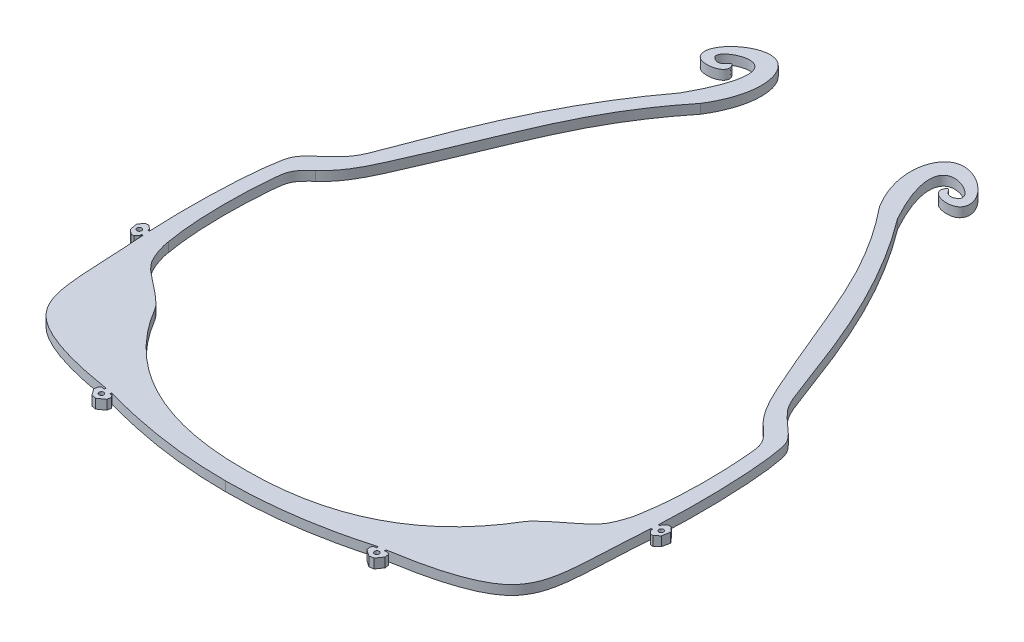
SolidWorks part; units mm, degrees
ref_plane "Front Plane" through (0, 0, 0) normal (0, 0, 1) x (1, 0, 0)
ref_plane "Top Plane" through (0, 0, 0) normal (0, 1, 0) x (1, 0, 0)
ref_plane "Right Plane" through (0, 0, 0) normal (1, 0, 0) x (0, 0, -1)
sketch "Sketch1" plane through (0, 0, 0) normal (0, 1, 0) x (1, 0, 0)
  line L0 (-56.7342, 4649.685) -> (-54.3432, 4649.8666)
  line L1 (-54.3432, 4649.8666) -> (-51.9673, 4650.1279)
  line L2 (-51.9673, 4650.1279) -> (-49.6128, 4650.4904)
  line L3 (-49.6128, 4650.4904) -> (-47.2873, 4650.9763)
  line L4 (-47.2873, 4650.9763) -> (-45.0028, 4651.606)
  line L5 (-45.0028, 4651.606) -> (-42.7754, 4652.393)
  line L6 (-42.7754, 4652.393) -> (-40.6236, 4653.3398)
  line L7 (-40.6236, 4653.3398) -> (-38.5569, 4654.4471)
  line L8 (-38.5569, 4654.4471) -> (-36.5628, 4655.7048)
  line L9 (-36.5628, 4655.7048) -> (-34.628, 4657.0886)
  line L10 (-34.628, 4657.0886) -> (-32.7572, 4658.5809)
  line L11 (-32.7572, 4658.5809) -> (-31.8781, 4659.3559)
  line L12 (-31.8781, 4659.3559) -> (-31.0378, 4660.1663)
  line L13 (-31.0378, 4660.1663) -> (-30.2434, 4661.0133)
  line L14 (-30.2434, 4661.0133) -> (-29.4929, 4661.8977)
  line L15 (-29.4929, 4661.8977) -> (-28.0377, 4663.8002)
  line L16 (-28.0377, 4663.8002) -> (-26.6418, 4665.7643)
  line L17 (-26.6418, 4665.7643) -> (-25.2842, 4667.7433)
  line L18 (-25.2842, 4667.7433) -> (-24.5616, 4668.7671)
  line L19 (-24.5616, 4668.7671) -> (-24.1207, 4669.3049)
  line L20 (-24.1207, 4669.3049) -> (-23.6287, 4669.8041)
  line L21 (-23.6287, 4669.8041) -> (-22.6527, 4670.6453)
  line L22 (-22.6527, 4670.6453) -> (-21.6624, 4671.4168)
  line L23 (-21.6624, 4671.4168) -> (-19.7154, 4672.8766)
  line L24 (-19.7154, 4672.8766) -> (-18.7888, 4673.6051)
  line L25 (-18.7888, 4673.6051) -> (-17.9151, 4674.3646)
  line L26 (-17.9151, 4674.3646) -> (-17.0961, 4675.1711)
  line L27 (-17.0961, 4675.1711) -> (-16.3332, 4676.0235)
  line L28 (-16.3332, 4676.0235) -> (-14.888, 4677.8872)
  line L29 (-14.888, 4677.8872) -> (-14.2651, 4678.8282)
  line L30 (-14.2651, 4678.8282) -> (-13.7395, 4679.8092)
  line L31 (-13.7395, 4679.8092) -> (-13.3157, 4680.8364)
  line L32 (-13.3157, 4680.8364) -> (-12.9921, 4681.9053)
  line L33 (-12.9921, 4681.9053) -> (-12.765, 4683.0137)
  line L34 (-12.765, 4683.0137) -> (-12.6116, 4684.156)
  line L35 (-12.6116, 4684.156) -> (-12.4221, 4686.5439)
  line L36 (-12.4221, 4686.5439) -> (-12.3049, 4688.9547)
  line L37 (-12.3049, 4688.9547) -> (-12.23, 4691.3606)
  line L38 (-12.23, 4691.3606) -> (-12.2173, 4693.7469)
  line L39 (-12.2173, 4693.7469) -> (-12.2979, 4696.128)
  line L40 (-12.2979, 4696.128) -> (-12.4621, 4698.525)
  line L41 (-12.4621, 4698.525) -> (-12.9016, 4703.3562)
  line L42 (-12.9016, 4703.3562) -> (-13.1725, 4705.7323)
  line L43 (-13.1725, 4705.7323) -> (-13.359, 4706.8497)
  line L44 (-13.359, 4706.8497) -> (-13.6464, 4707.8976)
  line L45 (-13.6464, 4707.8976) -> (-13.8331, 4708.3435)
  line L46 (-13.8331, 4708.3435) -> (-14.0727, 4708.7863)
  line L47 (-14.0727, 4708.7863) -> (-14.3603, 4709.2104)
  line L48 (-14.3603, 4709.2104) -> (-14.6922, 4709.6118)
  line L49 (-14.6922, 4709.6118) -> (-15.5352, 4710.4427)
  line L50 (-15.5352, 4710.4427) -> (-16.4733, 4711.2489)
  line L51 (-16.4733, 4711.2489) -> (-18.3969, 4712.8768)
  line L52 (-18.3969, 4712.8768) -> (-19.3317, 4713.7593)
  line L53 (-19.3317, 4713.7593) -> (-19.7964, 4714.2738)
  line L54 (-19.7964, 4714.2738) -> (-20.226, 4714.8564)
  line L55 (-20.226, 4714.8564) -> (-20.8491, 4716.0227)
  line L56 (-20.8491, 4716.0227) -> (-21.3607, 4717.2182)
  line L57 (-21.3607, 4717.2182) -> (-22.2565, 4719.6128)
  line L58 (-22.2565, 4719.6128) -> (-23.9365, 4724.4003)
  line L59 (-23.9365, 4724.4003) -> (-24.8142, 4726.6925)
  line L60 (-24.8142, 4726.6925) -> (-25.7235, 4728.951)
  line L61 (-25.7235, 4728.951) -> (-29.4192, 4737.978)
  line L62 (-29.4192, 4737.978) -> (-31.3112, 4742.476)
  line L63 (-31.3112, 4742.476) -> (-32.3108, 4744.6883)
  line L64 (-32.3108, 4744.6883) -> (-33.3653, 4746.8748)
  line L65 (-33.3653, 4746.8748) -> (-34.484, 4749.0197)
  line L66 (-34.484, 4749.0197) -> (-35.6822, 4751.1089)
  line L67 (-35.6822, 4751.1089) -> (-36.9697, 4753.1376)
  line L68 (-36.9697, 4753.1376) -> (-38.335, 4755.1176)
  line L69 (-38.335, 4755.1176) -> (-39.7566, 4757.0561)
  line L70 (-39.7566, 4757.0561) -> (-41.2239, 4758.9538)
  line L71 (-41.2239, 4758.9538) -> (-44.2837, 4762.6862)
  line L72 (-44.2837, 4762.6862) -> (-45.0093, 4763.5782)
  line L73 (-45.7102, 4766.0333) -> (-45.6003, 4766.895)
  line L74 (-44.3387, 4767.2717) -> (-41.5099, 4763.9631)
  line L75 (-41.5099, 4763.9631) -> (-39.7615, 4761.7893)
  line L76 (-39.7615, 4761.7893) -> (-36.1552, 4757.1077)
  line L77 (-36.1552, 4757.1077) -> (-34.4224, 4754.6956)
  line L78 (-34.4224, 4754.6956) -> (-32.818, 4752.1875)
  line L79 (-32.818, 4752.1875) -> (-31.4001, 4749.5854)
  line L80 (-31.4001, 4749.5854) -> (-30.1172, 4746.945)
  line L81 (-30.1172, 4746.945) -> (-27.7453, 4741.6402)
  line L82 (-27.7453, 4741.6402) -> (-25.4835, 4736.2816)
  line L83 (-25.4835, 4736.2816) -> (-23.2904, 4730.8724)
  line L84 (-23.2904, 4730.8724) -> (-21.1708, 4725.4153)
  line L85 (-21.1708, 4725.4153) -> (-19.1018, 4719.943)
  line L86 (-19.1018, 4719.943) -> (-18.1004, 4717.2034)
  line L87 (-18.1004, 4717.2034) -> (-17.875, 4716.5966)
  line L88 (-17.875, 4716.5966) -> (-17.6236, 4716.1359)
  line L89 (-17.6236, 4716.1359) -> (-17.2675, 4715.7336)
  line L90 (-17.2675, 4715.7336) -> (-16.7845, 4715.2999)
  line L91 (-16.7845, 4715.2999) -> (-14.566, 4713.4273)
  line L92 (-14.566, 4713.4273) -> (-13.4359, 4712.453)
  line L93 (-13.4359, 4712.453) -> (-12.2875, 4711.3506)
  line L94 (-12.2875, 4711.3506) -> (-11.7288, 4710.5494)
  line L95 (-11.7288, 4710.5494) -> (-11.4049, 4709.6505)
  line L96 (-11.4049, 4709.6505) -> (-11.1035, 4708.0976)
  line L97 (-11.1035, 4708.0976) -> (-10.7039, 4705.1867)
  line L98 (-10.7039, 4705.1867) -> (-10.3782, 4702.2301)
  line L99 (-10.3782, 4702.2301) -> (-10.1381, 4699.312)
  line L100 (-10.1381, 4699.312) -> (-9.9526, 4696.4059)
  line L101 (-9.9526, 4696.4059) -> (-9.8234, 4693.4642)
  line L102 (-9.8234, 4693.4642) -> (-9.7818, 4690.5097)
  line L103 (-9.7818, 4690.5097) -> (-9.8395, 4687.5651)
  line L104 (-9.8395, 4687.5651) -> (-10.1467, 4681.8499)
  line L105 (-10.2187, 4680.4106) -> (-10.5778, 4674.8324)
  line L106 (-10.5778, 4674.8324) -> (-10.9255, 4669.1921)
  line L107 (-10.9255, 4669.1921) -> (-11.1085, 4666.3239)
  line L108 (-11.1085, 4666.3239) -> (-11.3672, 4663.3976)
  line L109 (-11.3672, 4663.3976) -> (-11.5954, 4661.8877)
  line L110 (-11.5954, 4661.8877) -> (-11.9481, 4660.3817)
  line L111 (-11.9481, 4660.3817) -> (-12.469, 4658.9063)
  line L112 (-12.469, 4658.9063) -> (-13.1768, 4657.5086)
  line L113 (-13.1768, 4657.5086) -> (-14.0475, 4656.2056)
  line L114 (-14.0475, 4656.2056) -> (-15.0678, 4655.0233)
  line L115 (-15.0678, 4655.0233) -> (-15.6664, 4654.4674)
  line L116 (-15.6664, 4654.4674) -> (-16.3022, 4653.9611)
  line L117 (-16.3022, 4653.9611) -> (-17.6055, 4653.1269)
  line L118 (-17.6055, 4653.1269) -> (-18.9712, 4652.4383)
  line L119 (-18.9712, 4652.4383) -> (-20.3502, 4651.8561)
  line L120 (-20.3502, 4651.8561) -> (-21.7405, 4651.3486)
  line L121 (-21.7405, 4651.3486) -> (-23.1491, 4650.8937)
  line L122 (-23.1491, 4650.8937) -> (-25.9685, 4650.1281)
  line L123 (-25.9685, 4650.1281) -> (-28.8127, 4649.495)
  line L124 (-28.8127, 4649.495) -> (-34.3611, 4648.4388)
  line L125 (-35.7786, 4648.1905) -> (-42.1243, 4647.1501)
  line L126 (-42.1243, 4647.1501) -> (-45.3893, 4646.7207)
  line L127 (-45.3893, 4646.7207) -> (-48.6635, 4646.3827)
  line L128 (-48.6635, 4646.3827) -> (-55.1892, 4645.922)
  line L129 (-55.1892, 4645.922) -> (-61.7354, 4645.5886)
  line L130 (-61.7354, 4645.5886) -> (-63.9666, 4645.5453)
  line L131 (-63.9667, 4649.4865) -> (-59.1315, 4649.5688)
  line L132 (-59.1315, 4649.5688) -> (-56.7342, 4649.685)
  line L133 (-9.7721, 4681.8294) -> (-9.752, 4682.186)
  line L134 (-9.752, 4682.186) -> (-9.3693, 4682.5229)
  line L135 (-9.3693, 4682.5229) -> (-8.649, 4682.4768)
  line L136 (-8.649, 4682.4768) -> (-7.9775, 4681.713)
  line L137 (-7.9775, 4681.713) -> (-8.2411, 4680.2884)
  line L138 (-8.2411, 4680.2884) -> (-9.0059, 4679.6162)
  line L139 (-9.0059, 4679.6162) -> (-9.5491, 4679.6473)
  line L140 (-9.5491, 4679.6473) -> (-9.8867, 4680.0303)
  line L141 (-9.8867, 4680.0303) -> (-9.8664, 4680.3889)
  line L142 (-9.7721, 4681.8294) -> (-9.752, 4682.186)
  line L151 (-34.2991, 4648.0806) -> (-33.9447, 4648.1421)
  line L152 (-33.9447, 4648.1421) -> (-33.5285, 4647.8485)
  line L153 (-33.5285, 4647.8485) -> (-33.4056, 4647.1395)
  line L154 (-33.4056, 4647.1395) -> (-33.9931, 4646.3074)
  line L155 (-33.9931, 4646.3074) -> (-35.4108, 4646.0612)
  line L156 (-35.4108, 4646.0612) -> (-36.2441, 4646.6493)
  line L157 (-36.2441, 4646.6493) -> (-36.3669, 4647.358)
  line L158 (-36.3669, 4647.358) -> (-36.0733, 4647.7743)
  line L159 (-36.0733, 4647.7743) -> (-35.7187, 4647.8357)
  line L160 (-10.1467, 4681.8499) -> (-9.7721, 4681.8294)
  line L161 (-34.3611, 4648.4388) -> (-34.2991, 4648.0806)
  line L162 (-35.7786, 4648.1905) -> (-35.7187, 4647.8357)
  line L163 (-9.8664, 4680.3889) -> (-10.2187, 4680.4106)
  line L165 (-118.1813, 4682.186) -> (-118.5641, 4682.5226)
  line L166 (-118.5641, 4682.5226) -> (-119.2843, 4682.4768)
  line L167 (-119.2843, 4682.4768) -> (-119.9558, 4681.7128)
  line L168 (-119.9558, 4681.7128) -> (-119.8643, 4680.2786)
  line L169 (-119.8643, 4680.2786) -> (-119.0995, 4679.6064)
  line L170 (-119.0995, 4679.6064) -> (-118.3843, 4679.6471)
  line L171 (-118.3843, 4679.6471) -> (-118.0466, 4680.0303)
  line L172 (-118.0466, 4680.0303) -> (-118.0672, 4680.3889)
  line L173 (-118.0672, 4680.3889) -> (-117.7148, 4680.4103)
  line L174 (-117.7148, 4680.4103) -> (-117.3555, 4674.8322)
  line L175 (-117.3555, 4674.8322) -> (-117.0078, 4669.1921)
  line L176 (-117.0078, 4669.1921) -> (-116.8249, 4666.3237)
  line L177 (-116.8249, 4666.3237) -> (-116.566, 4663.3974)
  line L178 (-116.566, 4663.3974) -> (-116.3378, 4661.8875)
  line L179 (-116.3378, 4661.8875) -> (-115.9851, 4660.3817)
  line L180 (-115.9851, 4660.3817) -> (-115.4645, 4658.906)
  line L181 (-115.4645, 4658.906) -> (-114.7563, 4657.5086)
  line L182 (-114.7563, 4657.5086) -> (-113.8857, 4656.2053)
  line L183 (-113.8857, 4656.2053) -> (-112.8656, 4655.0233)
  line L184 (-112.8656, 4655.0233) -> (-112.2669, 4654.4674)
  line L185 (-112.2669, 4654.4674) -> (-111.6311, 4653.9608)
  line L186 (-111.6311, 4653.9608) -> (-110.328, 4653.1269)
  line L187 (-110.328, 4653.1269) -> (-108.9621, 4652.4383)
  line L188 (-108.9621, 4652.4383) -> (-107.5832, 4651.8561)
  line L189 (-107.5832, 4651.8561) -> (-106.1928, 4651.3484)
  line L190 (-106.1928, 4651.3484) -> (-104.7844, 4650.8937)
  line L191 (-104.7844, 4650.8937) -> (-101.9649, 4650.1279)
  line L192 (-101.9649, 4650.1279) -> (-99.1205, 4649.4948)
  line L193 (-99.1205, 4649.4948) -> (-93.5721, 4648.4388)
  line L194 (-93.5721, 4648.4388) -> (-93.6341, 4648.0806)
  line L195 (-93.6341, 4648.0806) -> (-93.9885, 4648.1421)
  line L196 (-93.9885, 4648.1421) -> (-94.4046, 4647.8485)
  line L197 (-94.4046, 4647.8485) -> (-94.5276, 4647.1392)
  line L198 (-94.5276, 4647.1392) -> (-93.9404, 4646.3074)
  line L199 (-93.9404, 4646.3074) -> (-92.5223, 4646.0612)
  line L200 (-92.5223, 4646.0612) -> (-91.6891, 4646.6493)
  line L201 (-91.6891, 4646.6493) -> (-91.5662, 4647.358)
  line L202 (-91.5662, 4647.358) -> (-91.8598, 4647.7743)
  line L203 (-91.8598, 4647.7743) -> (-92.2145, 4647.8357)
  line L204 (-92.1546, 4648.1905) -> (-92.2145, 4647.8357)
  line L205 (-92.1546, 4648.1905) -> (-85.8089, 4647.1501)
  line L206 (-85.8089, 4647.1501) -> (-82.5441, 4646.7204)
  line L207 (-82.5441, 4646.7204) -> (-79.2698, 4646.3827)
  line L208 (-79.2698, 4646.3827) -> (-72.7439, 4645.922)
  line L209 (-72.7439, 4645.922) -> (-66.1978, 4645.5886)
  line L210 (-66.1978, 4645.5886) -> (-63.9666, 4645.5453)
  line L211 (-63.9667, 4649.4865) -> (-68.8018, 4649.5688)
  line L212 (-68.8018, 4649.5688) -> (-71.1991, 4649.685)
  line L213 (-71.1991, 4649.685) -> (-73.5901, 4649.8666)
  line L214 (-73.5901, 4649.8666) -> (-75.9659, 4650.1279)
  line L215 (-75.9659, 4650.1279) -> (-78.3204, 4650.4904)
  line L216 (-78.3204, 4650.4904) -> (-80.646, 4650.976)
  line L217 (-80.646, 4650.976) -> (-82.9304, 4651.606)
  line L218 (-82.9304, 4651.606) -> (-85.1578, 4652.393)
  line L219 (-85.1578, 4652.393) -> (-87.3097, 4653.3398)
  line L220 (-87.3097, 4653.3398) -> (-89.3762, 4654.4469)
  line L221 (-89.3762, 4654.4469) -> (-91.3704, 4655.7045)
  line L222 (-91.3704, 4655.7045) -> (-93.3054, 4657.0883)
  line L223 (-93.3054, 4657.0883) -> (-95.1761, 4658.5809)
  line L224 (-95.1761, 4658.5809) -> (-96.0551, 4659.3559)
  line L225 (-96.0551, 4659.3559) -> (-96.8955, 4660.1661)
  line L226 (-96.8955, 4660.1661) -> (-97.6899, 4661.013)
  line L227 (-97.6899, 4661.013) -> (-98.4405, 4661.8974)
  line L228 (-98.4405, 4661.8974) -> (-99.8956, 4663.8003)
  line L229 (-99.8956, 4663.8003) -> (-101.2917, 4665.7643)
  line L230 (-101.2917, 4665.7643) -> (-102.649, 4667.7433)
  line L231 (-102.649, 4667.7433) -> (-103.3717, 4668.7671)
  line L232 (-103.3717, 4668.7671) -> (-103.8126, 4669.3049)
  line L233 (-103.8126, 4669.3049) -> (-104.3045, 4669.8038)
  line L234 (-104.3045, 4669.8038) -> (-105.2805, 4670.645)
  line L235 (-105.2805, 4670.645) -> (-106.2711, 4671.4168)
  line L236 (-106.2711, 4671.4168) -> (-108.218, 4672.8766)
  line L237 (-108.218, 4672.8766) -> (-109.1446, 4673.6051)
  line L238 (-109.1446, 4673.6051) -> (-110.0184, 4674.3646)
  line L239 (-110.0184, 4674.3646) -> (-110.8371, 4675.1711)
  line L240 (-110.8371, 4675.1711) -> (-111.6001, 4676.0232)
  line L241 (-111.6001, 4676.0232) -> (-113.0454, 4677.8872)
  line L242 (-113.0454, 4677.8872) -> (-113.6683, 4678.8282)
  line L243 (-113.6683, 4678.8282) -> (-114.1938, 4679.8092)
  line L244 (-114.1938, 4679.8092) -> (-114.6176, 4680.8364)
  line L245 (-114.6176, 4680.8364) -> (-114.9413, 4681.905)
  line L246 (-114.9413, 4681.905) -> (-115.1684, 4683.0135)
  line L247 (-115.1684, 4683.0135) -> (-115.3218, 4684.156)
  line L248 (-115.3218, 4684.156) -> (-115.5115, 4686.5436)
  line L249 (-115.5115, 4686.5436) -> (-115.6283, 4688.9545)
  line L250 (-115.6283, 4688.9545) -> (-115.7033, 4691.3606)
  line L251 (-115.7033, 4691.3606) -> (-115.7161, 4693.7466)
  line L252 (-115.7161, 4693.7466) -> (-115.6355, 4696.1278)
  line L253 (-115.6355, 4696.1278) -> (-115.4714, 4698.525)
  line L254 (-115.4714, 4698.525) -> (-115.0316, 4703.3562)
  line L255 (-115.0316, 4703.3562) -> (-114.7608, 4705.732)
  line L256 (-114.7608, 4705.732) -> (-114.5743, 4706.8497)
  line L257 (-114.5743, 4706.8497) -> (-114.287, 4707.8977)
  line L258 (-114.287, 4707.8977) -> (-114.1002, 4708.3435)
  line L259 (-114.1002, 4708.3435) -> (-113.8608, 4708.7862)
  line L260 (-113.8608, 4708.7862) -> (-113.5731, 4709.2103)
  line L261 (-113.5731, 4709.2103) -> (-113.2411, 4709.6117)
  line L262 (-113.2411, 4709.6117) -> (-112.3981, 4710.4425)
  line L263 (-112.3981, 4710.4425) -> (-111.4599, 4711.2487)
  line L264 (-111.4599, 4711.2487) -> (-109.5364, 4712.8767)
  line L265 (-109.5364, 4712.8767) -> (-108.602, 4713.7592)
  line L266 (-108.602, 4713.7592) -> (-108.1369, 4714.2737)
  line L267 (-108.1369, 4714.2737) -> (-107.7072, 4714.8564)
  line L268 (-107.7072, 4714.8564) -> (-107.0842, 4716.0225)
  line L269 (-107.0842, 4716.0225) -> (-106.5727, 4717.2181)
  line L270 (-106.5727, 4717.2181) -> (-105.6769, 4719.6127)
  line L271 (-105.6769, 4719.6127) -> (-103.9969, 4724.4001)
  line L272 (-103.9969, 4724.4001) -> (-103.1193, 4726.6924)
  line L273 (-103.1193, 4726.6924) -> (-102.2099, 4728.9509)
  line L274 (-102.2099, 4728.9509) -> (-98.5143, 4737.9778)
  line L275 (-98.5143, 4737.9778) -> (-96.6221, 4742.4757)
  line L276 (-96.6221, 4742.4757) -> (-95.6227, 4744.6884)
  line L277 (-95.6227, 4744.6884) -> (-94.5682, 4746.8748)
  line L278 (-94.5682, 4746.8748) -> (-93.4493, 4749.0197)
  line L279 (-93.4493, 4749.0197) -> (-92.2515, 4751.1088)
  line L280 (-92.2515, 4751.1088) -> (-90.9637, 4753.1374)
  line L281 (-90.9637, 4753.1374) -> (-89.5985, 4755.1174)
  line L282 (-89.5985, 4755.1174) -> (-88.177, 4757.0561)
  line L283 (-88.177, 4757.0561) -> (-86.7094, 4758.9538)
  line L284 (-86.7094, 4758.9538) -> (-83.65, 4762.6862)
  line L285 (-83.65, 4762.6862) -> (-82.924, 4763.5782)
  line L286 (-82.2232, 4766.0334) -> (-82.3333, 4766.8949)
  line L287 (-83.5948, 4767.2716) -> (-86.4235, 4763.963)
  line L288 (-86.4235, 4763.963) -> (-88.172, 4761.7894)
  line L289 (-88.172, 4761.7894) -> (-91.7784, 4757.1074)
  line L290 (-91.7784, 4757.1074) -> (-93.5112, 4754.6958)
  line L291 (-93.5112, 4754.6958) -> (-95.1154, 4752.1875)
  line L292 (-95.1154, 4752.1875) -> (-96.5333, 4749.5852)
  line L293 (-96.5333, 4749.5852) -> (-97.8162, 4746.9449)
  line L294 (-97.8162, 4746.9449) -> (-100.1881, 4741.6403)
  line L295 (-100.1881, 4741.6403) -> (-102.4501, 4736.2814)
  line L296 (-102.4501, 4736.2814) -> (-104.6429, 4730.8726)
  line L297 (-104.6429, 4730.8726) -> (-106.7626, 4725.415)
  line L298 (-106.7626, 4725.415) -> (-108.8314, 4719.9429)
  line L299 (-108.8314, 4719.9429) -> (-109.8329, 4717.2035)
  line L300 (-109.8329, 4717.2035) -> (-110.0583, 4716.5964)
  line L301 (-110.0583, 4716.5964) -> (-110.3097, 4716.1357)
  line L302 (-110.3097, 4716.1357) -> (-110.6661, 4715.7335)
  line L303 (-110.6661, 4715.7335) -> (-111.1489, 4715.2998)
  line L304 (-111.1489, 4715.2998) -> (-113.3676, 4713.4272)
  line L305 (-113.3676, 4713.4272) -> (-114.4976, 4712.4528)
  line L306 (-114.4976, 4712.4528) -> (-115.646, 4711.3505)
  line L307 (-115.646, 4711.3505) -> (-116.2044, 4710.5493)
  line L308 (-116.2044, 4710.5493) -> (-116.5286, 4709.6504)
  line L309 (-116.5286, 4709.6504) -> (-116.8298, 4708.0975)
  line L310 (-116.8298, 4708.0975) -> (-117.2296, 4705.1868)
  line L311 (-117.2296, 4705.1868) -> (-117.5553, 4702.2301)
  line L312 (-117.5553, 4702.2301) -> (-117.7952, 4699.312)
  line L313 (-117.7952, 4699.312) -> (-117.981, 4696.4059)
  line L314 (-117.981, 4696.4059) -> (-118.11, 4693.4642)
  line L315 (-118.11, 4693.4642) -> (-118.1516, 4690.5097)
  line L316 (-118.1516, 4690.5097) -> (-118.0939, 4687.5649)
  line L317 (-118.0939, 4687.5649) -> (-117.7865, 4681.8497)
  line L318 (-117.7865, 4681.8497) -> (-118.1612, 4681.8294)
  line L319 (-118.1612, 4681.8294) -> (-118.1813, 4682.186)
  spline S0 degree 3 poles (-45.7102, 4766.0333) (-45.8224, 4765.1537) (-45.5692, 4764.2663) (-45.0093, 4763.5782) knots 0 0 0 0 1 1 1 1
  spline S1 degree 3 poles (-44.3387, 4767.2717) (-44.5973, 4767.574) (-45.0517, 4767.6095) (-45.3539, 4767.351) knots 0 0 0 0 1 1 1 1
  spline S2 degree 3 poles (-45.3539, 4767.351) (-45.4898, 4767.2349) (-45.5777, 4767.0723) (-45.6003, 4766.895) knots 0 0 0 0 1 1 1 1
  spline S3 degree 3 poles (-82.924, 4763.5782) (-82.3642, 4764.2661) (-82.111, 4765.1536) (-82.2232, 4766.0334) knots 0 0 0 0 1 1 1 1
  spline S4 degree 3 poles (-82.3333, 4766.8949) (-82.3835, 4767.2894) (-82.7441, 4767.5683) (-83.1386, 4767.518) knots 0 0 0 0 1 1 1 1
  spline S5 degree 3 poles (-83.1386, 4767.518) (-83.3159, 4767.4954) (-83.4785, 4767.4075) (-83.5948, 4767.2716) knots 0 0 0 0 1 1 1 1
  point P0 (-118.266, 4681.8497)
sketch "Sketch2" plane through (0, 0, 0) normal (0, 1, 0) x (1, 0, 0)
  line L0 (-63.9497, 4644.1023) -> (-63.9497, 4616.7817) construction
  line L1 (-93.82, 4645.684) -> (-92.8569, 4645.5109)
  line L2 (-94.7844, 4647.0501) -> (-93.82, 4645.684)
  line L3 (-94.6391, 4647.8883) -> (-94.7844, 4647.0501)
  line L4 (-94.2154, 4648.1872) -> (-94.6391, 4647.8883)
  line L5 (-93.6004, 4648.0806) -> (-94.2154, 4648.1872)
  line L6 (-93.5721, 4648.4388) -> (-93.6004, 4648.0806)
  line L7 (-92.1208, 4648.1905) -> (-92.2145, 4647.8357)
  line L8 (-91.6541, 4647.7387) -> (-92.2145, 4647.8357)
  line L9 (-91.3389, 4647.2917) -> (-91.6541, 4647.7387)
  line L10 (-91.4789, 4646.4833) -> (-91.3389, 4647.2917)
  line L11 (-92.8569, 4645.5109) -> (-91.4789, 4646.4833)
  line L12 (-118.033, 4680.3889) -> (-117.7145, 4680.4106)
  line L13 (-118.0127, 4680.0303) -> (-118.033, 4680.3889)
  line L14 (-118.6203, 4679.341) -> (-118.0127, 4680.0303)
  line L15 (-119.1822, 4679.3088) -> (-118.6203, 4679.341)
  line L16 (-120.1486, 4680.1583) -> (-119.1822, 4679.3088)
  line L17 (-120.4548, 4681.813) -> (-120.1486, 4680.1583)
  line L18 (-119.5704, 4682.8189) -> (-120.4548, 4681.813)
  line L19 (-118.9142, 4682.861) -> (-119.5704, 4682.8189)
  line L20 (-118.1474, 4682.186) -> (-118.9142, 4682.861)
  line L21 (-118.1273, 4681.8294) -> (-118.1474, 4682.186)
  line L22 (-117.7865, 4681.8499) -> (-118.1273, 4681.8294)
  line L980 (-10.113, 4681.8499) -> (-9.7721, 4681.8294)
  line L981 (-9.7721, 4681.8294) -> (-9.752, 4682.186)
  line L982 (-9.752, 4682.186) -> (-8.9852, 4682.861)
  line L983 (-8.9852, 4682.861) -> (-8.329, 4682.8189)
  line L984 (-8.329, 4682.8189) -> (-7.4446, 4681.813)
  line L985 (-7.4446, 4681.813) -> (-7.7508, 4680.1583)
  line L986 (-7.7508, 4680.1583) -> (-8.7173, 4679.3088)
  line L987 (-8.7173, 4679.3088) -> (-9.2791, 4679.341)
  line L988 (-9.2791, 4679.341) -> (-9.8867, 4680.0303)
  line L989 (-9.8867, 4680.0303) -> (-9.8664, 4680.3889)
  line L990 (-9.8664, 4680.3889) -> (-10.185, 4680.4106)
  line L991 (-35.0425, 4645.5109) -> (-36.4205, 4646.4833)
  line L992 (-36.4205, 4646.4833) -> (-36.5605, 4647.2917)
  line L993 (-36.5605, 4647.2917) -> (-36.2453, 4647.7387)
  line L994 (-36.2453, 4647.7387) -> (-35.685, 4647.8357)
  line L995 (-35.7786, 4648.1905) -> (-35.685, 4647.8357)
  line L996 (-34.3274, 4648.4388) -> (-34.2991, 4648.0806)
  line L997 (-34.2991, 4648.0806) -> (-33.6841, 4648.1872)
  line L998 (-33.6841, 4648.1872) -> (-33.2603, 4647.8883)
  line L999 (-33.2603, 4647.8883) -> (-33.1151, 4647.0501)
  line L1000 (-33.1151, 4647.0501) -> (-34.0794, 4645.684)
  line L1001 (-34.0794, 4645.684) -> (-35.0425, 4645.5109)
  circle A0 centre (-8.7173, 4681.067) radius 0.5
  circle A1 centre (-34.8039, 4646.968) radius 0.5
  circle A2 centre (-93.0956, 4646.968) radius 0.5
  circle A3 centre (-119.1822, 4681.067) radius 0.5
  spline S0 degree 2 poles (-92.1546, 4648.1905) (-63.9659, 4640.014) (-35.7786, 4648.1905) knots 0 0 0 1 1 1
  spline S1 degree 3 poles (-34.3274, 4648.4388) (-27.4327, 4649.5256) (-9.1783, 4653.9446) (-11.3752, 4665.2471) (-10.185, 4680.4106) knots 0 0 0 0 0.392232 1 1 1 1
  spline S2 degree 3 poles (-10.113, 4681.8499) (-9.5077, 4693.3169) (-10.3901, 4707.9822) (-12.561, 4712.366) (-17.5775, 4715.7567) (-22.7095, 4728.4645) (-28.5404, 4746.8382) (-40.9499, 4763.3475) knots 0 0 0 0 0.170778 0.204985 0.326837 0.407861 1 1 1 1
  spline S4 degree 2 poles (-63.9497, 4648.1905) (-36.8156, 4648.0467) (-24.8892, 4668.2552) knots 0 0 0 1 1 1
  spline S5 degree 3 poles (-24.8892, 4668.2552) (-23.6193, 4670.1519) (-17.6724, 4674.2298) (-16.6833, 4675.5601) (-15.4148, 4677.1136) (-14.2612, 4680.2386) (-14.0739, 4681.8499) knots 0 0 0 0 0.517385 0.711984 0.762678 1 1 1 1
  spline S6 degree 3 poles (-14.0739, 4681.8499) (-13.01, 4687.586) (-12.7265, 4697.7456) (-13.8878, 4707.9745) (-15.5715, 4709.6148) (-16.5698, 4710.5494) knots 0 0 0 0 0.7977 0.8977 1 1 1 1
  spline S7 degree 3 poles (-16.5698, 4710.5494) (-19.5964, 4713.0857) (-31.0152, 4737.8246) (-33.8839, 4749.6931) (-45.0093, 4763.5782) knots 0 0 0 0 0.147118 0.925748 0.925748 0.925748 0.925748
  spline S8 degree 3 poles (-40.9499, 4763.3475) (-44.3662, 4769.5252) (-46.6979, 4780.4443) (-35.866, 4774.6976) (-40.2212, 4772.1356) (-40.8007, 4774.931) (-42.5916, 4771.682) (-37.0995, 4770.5715) (-34.3415, 4775.7068) (-47.0029, 4785.5183) (-49.7025, 4771.1153) (-45.0093, 4763.5782) knots 0 0 0 0 0.048335 0.142928 0.16216 0.231927 0.259382 0.409256 0.461524 0.763332 1 1 1 1
  spline S9 degree 3 poles (-86.9496, 4763.3475) (-83.5333, 4769.5252) (-81.2016, 4780.4443) (-92.0334, 4774.6976) (-87.6783, 4772.1356) (-87.0988, 4774.931) (-85.3078, 4771.682) (-90.8, 4770.5715) (-93.558, 4775.7068) (-80.8966, 4785.5183) (-78.1969, 4771.1153) (-82.8901, 4763.5782) knots 0 0 0 0 0.048335 0.142928 0.16216 0.231927 0.259382 0.409256 0.461524 0.763332 1 1 1 1
  spline S10 degree 3 poles (-111.3296, 4710.5494) (-108.3031, 4713.0857) (-96.8843, 4737.8246) (-94.0156, 4749.6931) (-82.8901, 4763.5782) knots 0 0 0 0 0.147118 0.925748 0.925748 0.925748 0.925748
  spline S11 degree 3 poles (-113.8255, 4681.8499) (-114.8894, 4687.586) (-115.173, 4697.7456) (-114.0117, 4707.9745) (-112.3279, 4709.6148) (-111.3296, 4710.5494) knots 0 0 0 0 0.7977 0.8977 1 1 1 1
  spline S12 degree 3 poles (-103.0103, 4668.2552) (-104.2802, 4670.1519) (-110.2271, 4674.2298) (-111.2161, 4675.5601) (-112.4846, 4677.1136) (-113.6382, 4680.2386) (-113.8255, 4681.8499) knots 0 0 0 0 0.517385 0.711984 0.762678 1 1 1 1
  spline S13 degree 2 poles (-63.9497, 4648.1905) (-91.0839, 4648.0467) (-103.0103, 4668.2552) knots 0 0 0 1 1 1
  spline S14 degree 3 poles (-117.7865, 4681.8499) (-118.3917, 4693.3169) (-117.5094, 4707.9822) (-115.3385, 4712.366) (-110.3219, 4715.7567) (-105.1899, 4728.4645) (-99.359, 4746.8382) (-86.9496, 4763.3475) knots 0 0 0 0 0.170778 0.204985 0.326837 0.407861 1 1 1 1
  spline S15 degree 3 poles (-93.5721, 4648.4388) (-100.4667, 4649.5256) (-118.7212, 4653.9446) (-116.5242, 4665.2471) (-117.7145, 4680.4106) knots 0 0 0 0 0.392232 1 1 1 1
  spline S16 degree 2 poles (-35.7449, 4648.1905) (-63.9335, 4640.014) (-92.1208, 4648.1905) knots 0 0 0 1 1 1
  point P7 (-63.8357, 4647.7743)
  point P18 (-63.9667, 4647.7743)
  point P19 (0, 0)
  point P24 (0, 0)
  point P26 (-45.142, 4775.813)
  point P27 (-27.6993, 4767.5639)
  point P28 (-33.5285, 4768.0571)
  point P29 (0, 0)
  point P30 (-25.3608, 4766.4208)
  point P31 (-45.0093, 4763.5782)
  point P32 (0, 0)
  point P34 (-40.6334, 4772.3392)
  point P35 (-37.6246, 4772.6559)
  point P36 (0, 0)
  point P37 (-35.7787, 4771.4524)
  point P40 (-41.221, 4774.771)
  point P41 (0, 0)
  point P92 (0, 0)
  point P93 (-36.367, 4772.1947)
  point P94 (0, 0)
  point P95 (0, 0)
  point P96 (0, 0)
  point P97 (0, 0)
  point P98 (-37.9924, 4772.986)
  point P99 (-41.3322, 4773.9402)
  point P100 (-34.8869, 4647.1583)
  point P101 (-34.8378, 4646.968)
  point P102 (-8.7173, 4681.067)
  point P103 (-14.1078, 4681.8499)
  point P104 (-16.6037, 4710.5494)
  point P105 (-14.1259, 4707.5292)
  point P106 (-17.9153, 4717.1696)
  point P107 (-44.6186, 4775.0823)
  point P108 (-38.4503, 4773.2382)
  point P109 (-63.9497, 4644.1023)
  dimension "D1" = 1
extrude "Boss-Extrude2" add sketch "Sketch2" along normal blind 2 separate body
